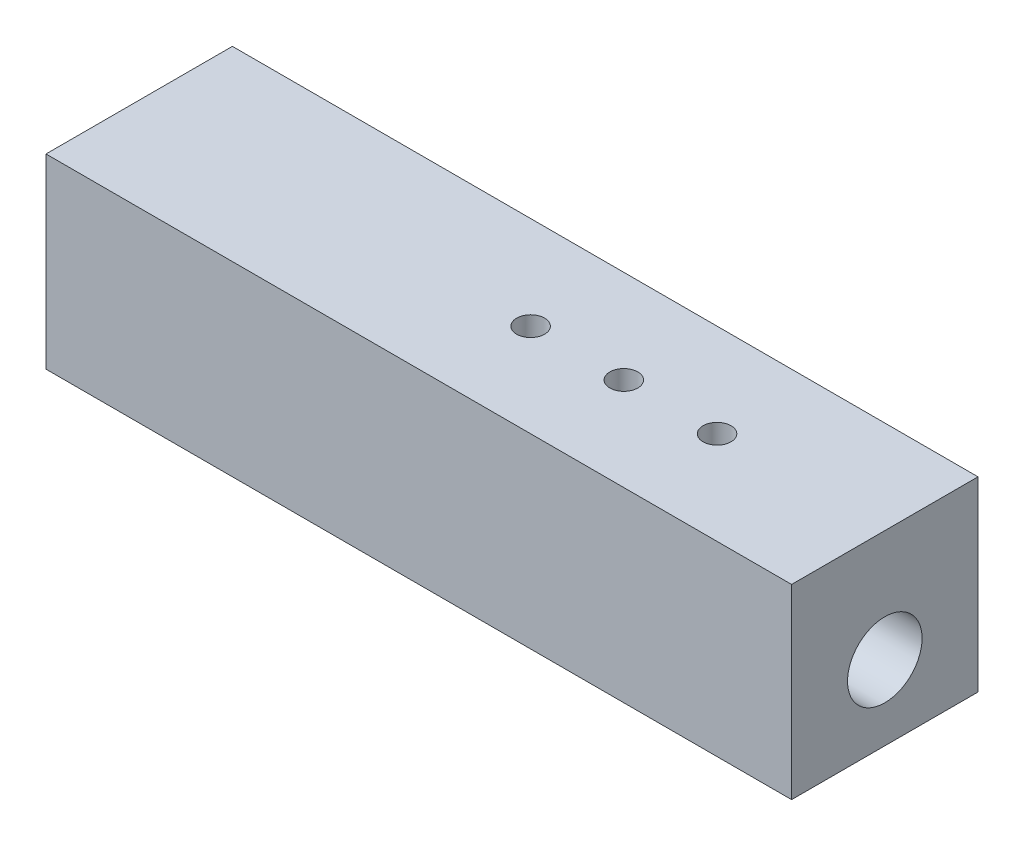
SolidWorks part; units mm, degrees
ref_plane "Front Plane" through (0, 0, 0) normal (0, 0, 1) x (1, 0, 0)
ref_plane "Top Plane" through (0, 0, 0) normal (0, 1, 0) x (1, 0, 0)
ref_plane "Right Plane" through (0, 0, 0) normal (1, 0, 0) x (0, 0, -1)
sketch "Sketch1" plane through (0, 0, 0) normal (0, 1, 0) x (1, 0, 0)
  line L1 (20, 5) -> (-20, 5)
  line L2 (20, 5) -> (20, -5)
  line L3 (20, -5) -> (-20, -5)
  line L4 (-20, 5) -> (-20, -5)
  line L5 (0, -5) -> (0, 5) construction
  line L6 (20, 0) -> (-20, 0) construction
  point P0 (0, 0)
  dimension "D1" = 10
  dimension "D2" = 40
extrude "Boss-Extrude1" add sketch "Sketch1" along normal blind 10
sketch "Sketch2" plane through (20, 0, 0) normal (1, 0, 0) x (0, 0, -1)
  line L0 (0, 0) -> (0, 4) construction
  line L1 (-5, 0) -> (5, 0) construction
  circle A0 centre (0, 4) radius 2
  dimension "D1" = 4
  dimension "D2" = 4
extrude "Cut-Extrude1" cut sketch "Sketch2" against normal through all
sketch "Sketch3" plane through (0, 10, 0) normal (0, 1, 0) x (1, 0, 0)
  line L0 (20, -5) -> (20, 5) construction
  line L2 (6, 0) -> (11, 0) construction
  line L3 (1, 0) -> (6, 0) construction
  circle A0 centre (11, 0) radius 0.75
  circle A1 centre (6, 0) radius 0.75
  circle A2 centre (1, 0) radius 0.75
  point P6 (-5.1516, -0.3515)
  point P10 (-3, 0)
  dimension "D3" = 1.5
  dimension "D1" = 5
  dimension "D2" = 9
  dimension "D4" = 5
extrude "Cut-Extrude2" cut sketch "Sketch3" against normal up to next
